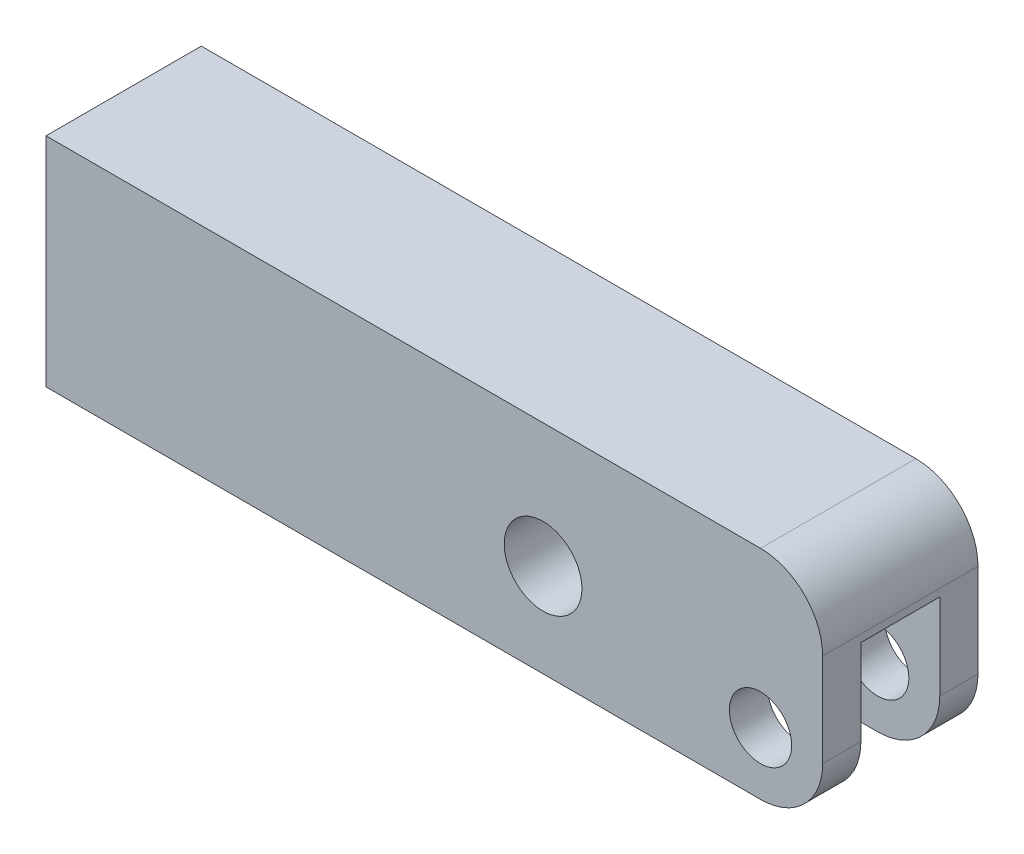
SolidWorks part; units mm, degrees
material "Alloy Steel"
ref_plane "Front Plane" through (0, 0, 0) normal (0, 0, 1) x (1, 0, 0)
ref_plane "Top Plane" through (0, 0, 0) normal (0, 1, 0) x (1, 0, 0)
ref_plane "Right Plane" through (0, 0, 0) normal (1, 0, 0) x (0, 0, -1)
sketch "Sketch11" plane through (0, 0, 0) normal (0, 0, 1) x (1, 0, 0)
  line L1 (-146.05, 31.75) -> (12.7, 31.75)
  line L2 (-146.05, 31.75) -> (-146.05, -12.7)
  line L3 (-146.05, -12.7) -> (12.7, -12.7)
  line L4 (12.7, 31.75) -> (12.7, -12.7)
  circle A0 centre (0, 0) radius 6.369
  circle A1 centre (-44.45, 6.35) radius 7.9438
  dimension "D1" = 12.7381
  dimension "D6" = 15.8877
  dimension "D2" = 12.7
  dimension "D3" = 146.05
  dimension "D4" = 44.45
  dimension "D5" = 44.45
  dimension "D7" = 12.7
  dimension "D8" = 6.35
extrude "Extrude3" add sketch "Sketch11" along normal mid plane 31.75
sketch "Sketch12" plane through (0, -12.7, 0) normal (0, -1, 0) x (1, 0, 0)
  line L0 (0, 0) -> (-16.2248, 0) construction
  line L1 (-17.526, 8.0645) -> (12.7, 8.0645)
  line L2 (12.7, 15.875) -> (12.7, -15.875) construction
  line L3 (12.7, 8.0645) -> (12.7, -8.0645)
  line L4 (-146.05, 15.875) -> (12.7, 15.875) construction
  line L5 (-17.526, -8.0645) -> (12.7, -8.0645)
  arc A0 (-17.526, 8.0645) -> (-17.526, -8.0645) centre (-17.526, 0) ccw
  dimension "D3" = 38.2905
  dimension "D1" = 16.129
  dimension "D2" = 7.8105
extrude "Cut-Extrude1" cut sketch "Sketch12" against normal blind 30.226
fillet "Fillet1" radius 12.7 3 edges at (12.7, 31.75, 0) (12.7, -12.7, -11.9697) (12.7, -12.7, 11.9697)
